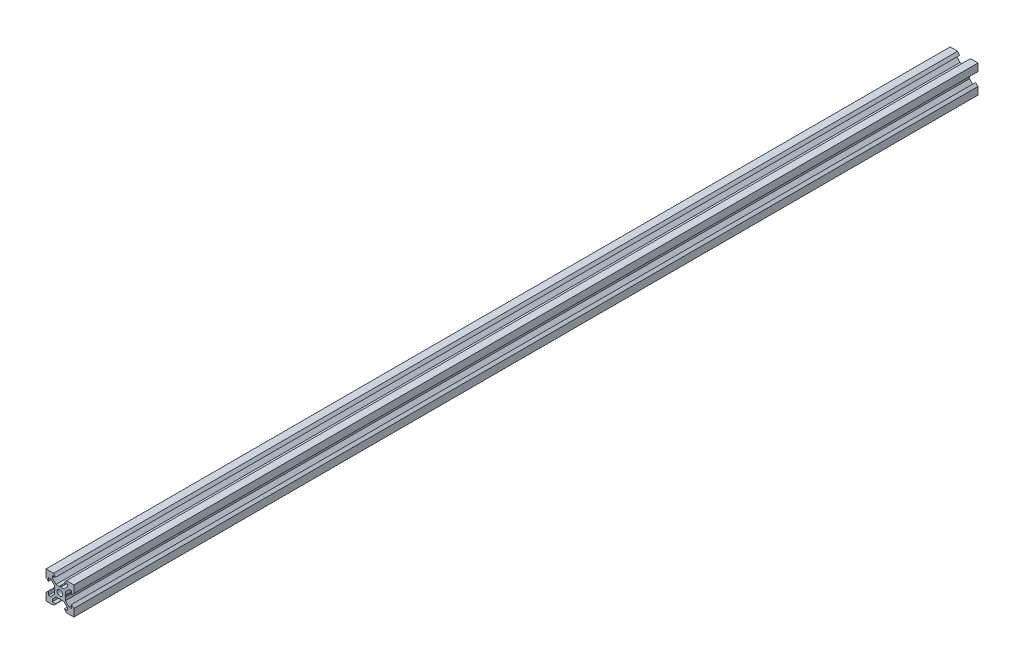
SolidWorks part; units mm, degrees
ref_plane "Front Plane" through (0, 0, 0) normal (0, 0, 1) x (1, 0, 0)
ref_plane "Top Plane" through (0, 0, 0) normal (0, 1, 0) x (1, 0, 0)
ref_plane "Right Plane" through (0, 0, 0) normal (1, 0, 0) x (0, 0, -1)
sketch "Sketch1" plane through (0, 0, 0) normal (0, 0, 1) x (1, 0, 0)
  line L0 (10, 10) -> (4.6104, 10) construction
  line L1 (10, 10) -> (10, 4.6104) construction
  line L2 (10, -10) -> (10, -4.6104) construction
  line L3 (10, -10) -> (4.6104, -10) construction
  line L4 (10, 10) -> (10, 4.6104)
  line L5 (6.5607, 5.5) -> (8.2, 5.5)
  line L6 (5.5, 8.2) -> (5.5, 6.5607)
  line L7 (10, 10) -> (4.6104, 10)
  line L8 (10, 10) -> (10, 4.6104)
  line L9 (6.5607, 5.5) -> (3.9, 2.8393)
  line L10 (5.5, 6.5607) -> (2.8393, 3.9)
  line L11 (10, 4.6104) -> (8.2, 3.1)
  line L12 (4.6104, 10) -> (3.1, 8.2)
  line L13 (8.2, 3.1) -> (8.2, 5.5)
  line L14 (3.1, 8.2) -> (5.5, 8.2)
  line L15 (-6.5607, 5.5) -> (-8.2, 5.5)
  line L16 (6.5607, -5.5) -> (8.2, -5.5)
  line L17 (3.1, -8.2) -> (5.5, -8.2)
  line L18 (8.2, -3.1) -> (8.2, -5.5)
  line L19 (4.6104, -10) -> (3.1, -8.2)
  line L20 (10, -4.6104) -> (8.2, -3.1)
  line L21 (0.5196, -3.9) -> (0, -3.6)
  line L22 (0.5196, 3.9) -> (0, 3.6)
  line L23 (3.6, 0) -> (3.9, -0.5196)
  line L24 (3.9, 0.5196) -> (3.6, 0)
  line L25 (3.9, 0.5196) -> (3.9, 2.8393)
  line L26 (2.8393, 3.9) -> (0.5196, 3.9)
  line L27 (3.9, -2.8393) -> (3.9, -0.5196)
  line L28 (2.8393, -3.9) -> (0.5196, -3.9)
  line L29 (5.5, -6.5607) -> (2.8393, -3.9)
  line L30 (6.5607, -5.5) -> (3.9, -2.8393)
  line L31 (10, -10) -> (10, -4.6104)
  line L32 (10, -10) -> (4.6104, -10)
  line L33 (5.5, -8.2) -> (5.5, -6.5607)
  line L34 (-6.5607, -5.5) -> (-8.2, -5.5)
  line L35 (10, -10) -> (10, -4.6104)
  line L36 (0, 0) -> (0, 8.2) construction
  line L37 (-10, -10) -> (-4.6104, -10) construction
  line L38 (-10, -10) -> (-10, -4.6104) construction
  line L39 (-10, 10) -> (-10, 4.6104) construction
  line L40 (-10, 10) -> (-4.6104, 10) construction
  line L41 (-10, -10) -> (-10, -4.6104)
  line L43 (-5.5, -8.2) -> (-5.5, -6.5607)
  line L44 (-10, -10) -> (-4.6104, -10)
  line L45 (-10, -10) -> (-10, -4.6104)
  line L46 (-6.5607, -5.5) -> (-3.9, -2.8393)
  line L47 (-5.5, -6.5607) -> (-2.8393, -3.9)
  line L48 (-2.8393, -3.9) -> (-0.5196, -3.9)
  line L49 (-3.9, -2.8393) -> (-3.9, -0.5196)
  line L50 (-2.8393, 3.9) -> (-0.5196, 3.9)
  line L51 (-3.9, 0.5196) -> (-3.9, 2.8393)
  line L52 (-3.9, 0.5196) -> (-3.6, 0)
  line L53 (-3.6, 0) -> (-3.9, -0.5196)
  line L54 (-0.5196, 3.9) -> (0, 3.6)
  line L55 (-0.5196, -3.9) -> (0, -3.6)
  line L56 (-10, -4.6104) -> (-8.2, -3.1)
  line L57 (-4.6104, -10) -> (-3.1, -8.2)
  line L58 (-8.2, -3.1) -> (-8.2, -5.5)
  line L59 (-3.1, -8.2) -> (-5.5, -8.2)
  line L60 (-10, -10) -> (10, -10) construction
  line L61 (-10, -10) -> (-10, 10) construction
  line L62 (-3.1, 8.2) -> (-5.5, 8.2)
  line L63 (-8.2, 3.1) -> (-8.2, 5.5)
  line L64 (-4.6104, 10) -> (-3.1, 8.2)
  line L65 (-10, 4.6104) -> (-8.2, 3.1)
  line L66 (-5.5, 6.5607) -> (-2.8393, 3.9)
  line L67 (-6.5607, 5.5) -> (-3.9, 2.8393)
  line L68 (-10, 10) -> (-10, 4.6104)
  line L69 (-10, 10) -> (-4.6104, 10)
  line L70 (-5.5, 8.2) -> (-5.5, 6.5607)
  line L71 (-10, 10) -> (10, 10) construction
  line L72 (-10, 10) -> (-10, 4.6104)
  line L73 (10, -10) -> (10, 10) construction
  line L74 (-10, -10) -> (10, 10) construction
  line L75 (-10, 10) -> (10, -10) construction
  circle A0 centre (0, 0) radius 2
  dimension "D7" = 4
  dimension "D1" = 20
  dimension "D2" = 5.3896
  dimension "D3" = 4.5
  dimension "D4" = 50
  dimension "D5" = 1.8
  dimension "D6" = 1.5104
  dimension "D8" = 5.5
  dimension "D9" = 120
  dimension "D10" = 0.3
  dimension "D11" = 2.3197
  dimension "D12" = 7.8
  dimension "D13" = 7.8
  dimension "D14" = 1.5
  dimension "D15" = 2.6607
extrude "Boss-Extrude1" add sketch "Sketch1" along normal mid plane 649.15 contours L70 L62 L64 L69 L68 L65 L63 L15 L67 L51 L52 L53 L49 L46 L34 L58 L56 L41 L44 L57 L59 L43 L47 L48 L55 L21 L28 L29 L33 L17 L19 L32 L31 L20 L18 L16 L30 L27 L23 L24 L25 L9 L5 L13 L11 L4 L7 L12 L14 L6 L10
